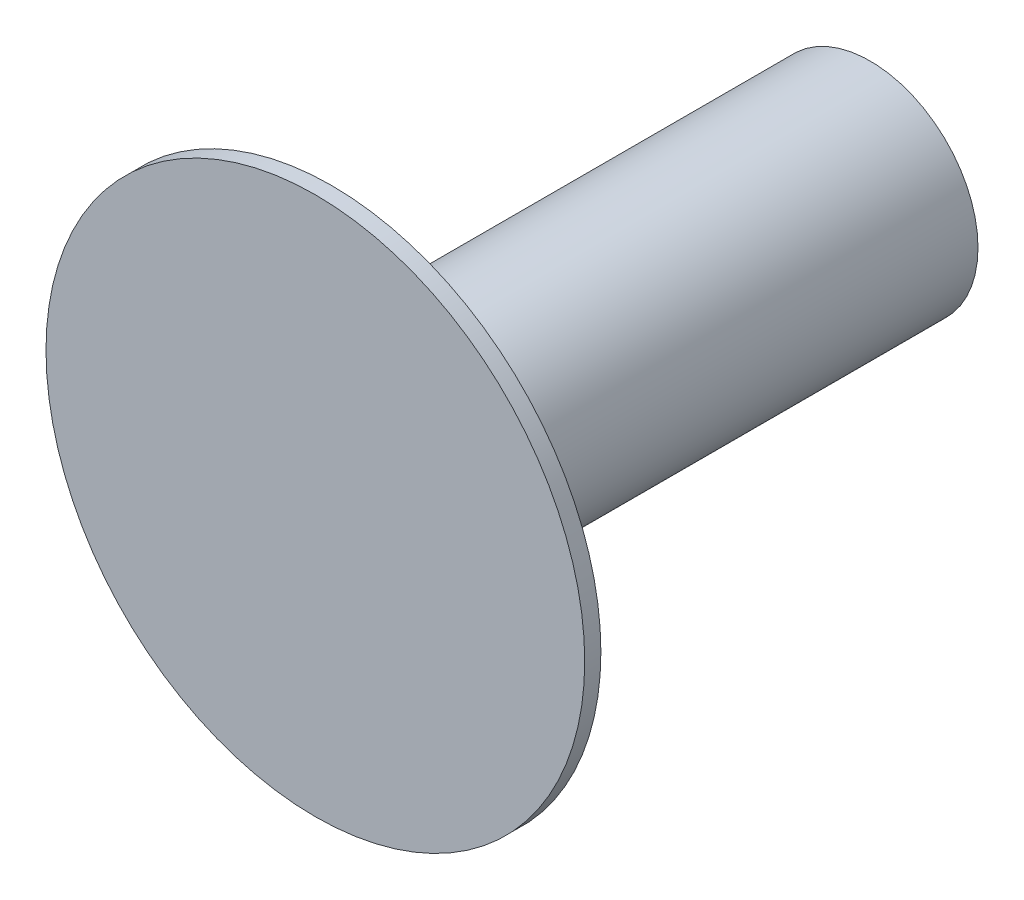
SolidWorks part; units mm, degrees
ref_plane "Front Plane" through (0, 0, 0) normal (0, 0, 1) x (1, 0, 0)
ref_plane "Top Plane" through (0, 0, 0) normal (0, 1, 0) x (1, 0, 0)
ref_plane "Right Plane" through (0, 0, 0) normal (1, 0, 0) x (0, 0, -1)
sketch "Sketch2" plane through (0, 0, 0) normal (0, 0, 1) x (1, 0, 0)
  circle A0 centre (0, 0) radius 10
  dimension "D1" = 20
extrude "Boss-Extrude1" add sketch "Sketch2" along normal blind 0.6
sketch "Sketch3" plane through (0, 0, 0) normal (0, 0, -1) x (-1, 0, 0)
  circle A0 centre (0, 0) radius 4
  dimension "D1" = 8
extrude "Boss-Extrude2" add sketch "Sketch3" along normal blind 20
